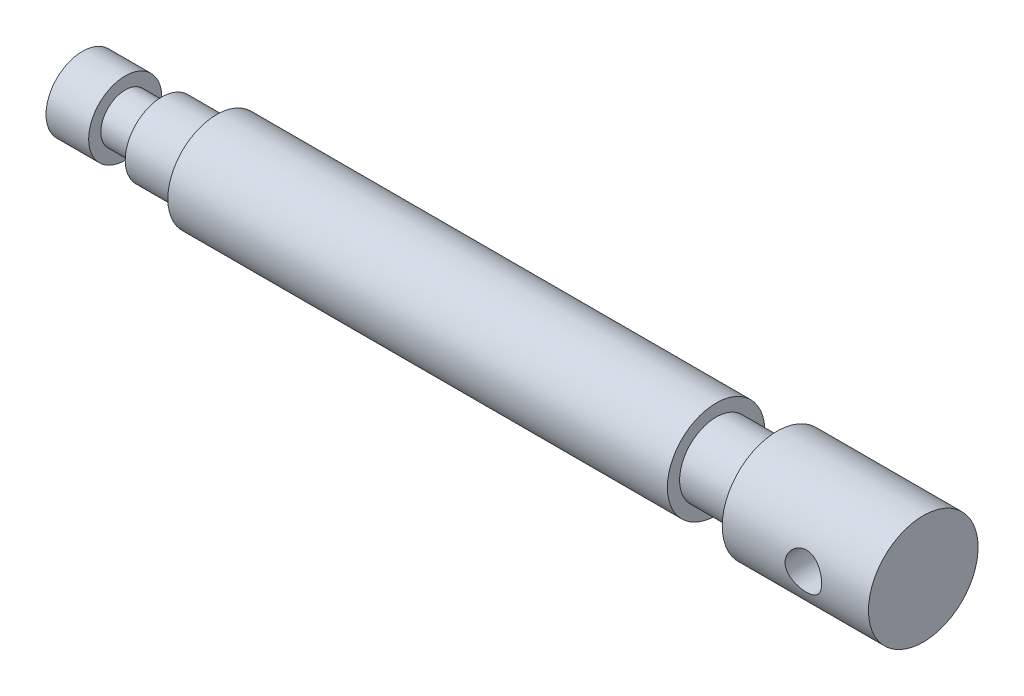
SolidWorks part; units mm, degrees
ref_plane "Front" through (0, 0, 0) normal (0, 0, 1) x (1, 0, 0)
ref_plane "Top" through (0, 0, 0) normal (0, 1, 0) x (1, 0, 0)
ref_plane "Right" through (0, 0, 0) normal (1, 0, 0) x (0, 0, -1)
sketch "Sketch2" plane through (0, 0, 0) normal (0, 0, 1) x (1, 0, 0)
  line L0 (0, 0) -> (0, 6)
  line L1 (0, 6) -> (7, 6)
  line L2 (7, 6) -> (7, 4)
  line L3 (7, 4) -> (13, 4)
  line L4 (13, 4) -> (13, 6)
  line L5 (13, 6) -> (22, 6)
  line L6 (22, 6) -> (22, 8)
  line L7 (22, 8) -> (104, 8)
  line L8 (104, 8) -> (104, 6)
  line L9 (104, 6) -> (114, 6)
  line L10 (114, 6) -> (114, 9)
  line L11 (114, 9) -> (138, 9)
  line L12 (138, 9) -> (138, 0)
  line L13 (-35.7429, 0) -> (167.4961, 0) construction
  line L14 (7, 4) -> (7, 0)
  line L15 (13, 4) -> (13, 0)
  line L17 (22, 0) -> (22, 6)
  line L18 (104, 6) -> (104, 0)
  line L20 (114, 0) -> (114, 6)
  arc A0 (123, 0) -> (129, 0) centre (126, 0) cw
  point P25 (0, 0)
  point P26 (126, 9)
  dimension "D1" = 138
  dimension "D11" = 3
  dimension "D2" = 82
  dimension "D3" = 10
  dimension "D4" = 6
  dimension "D5" = 4
  dimension "D6" = 8
  dimension "D7" = 9
  dimension "D8" = 6
  dimension "D9" = 7
  dimension "D10" = 9
revolve "Revolve1" add sketch "Sketch2" angle 360 about L13
ref_plane "Plane1" through (0, 0, 9) normal (0, 0, 1) x (1, 0, 0)
sketch "Sketch3" plane through (0, 0, 9) normal (0, 0, 1) x (1, 0, 0)
  circle A0 centre (127.3193, 0) radius 3
  dimension "D1" = 6
extrude "Cut-Extrude1" cut sketch "Sketch3" against normal through all
